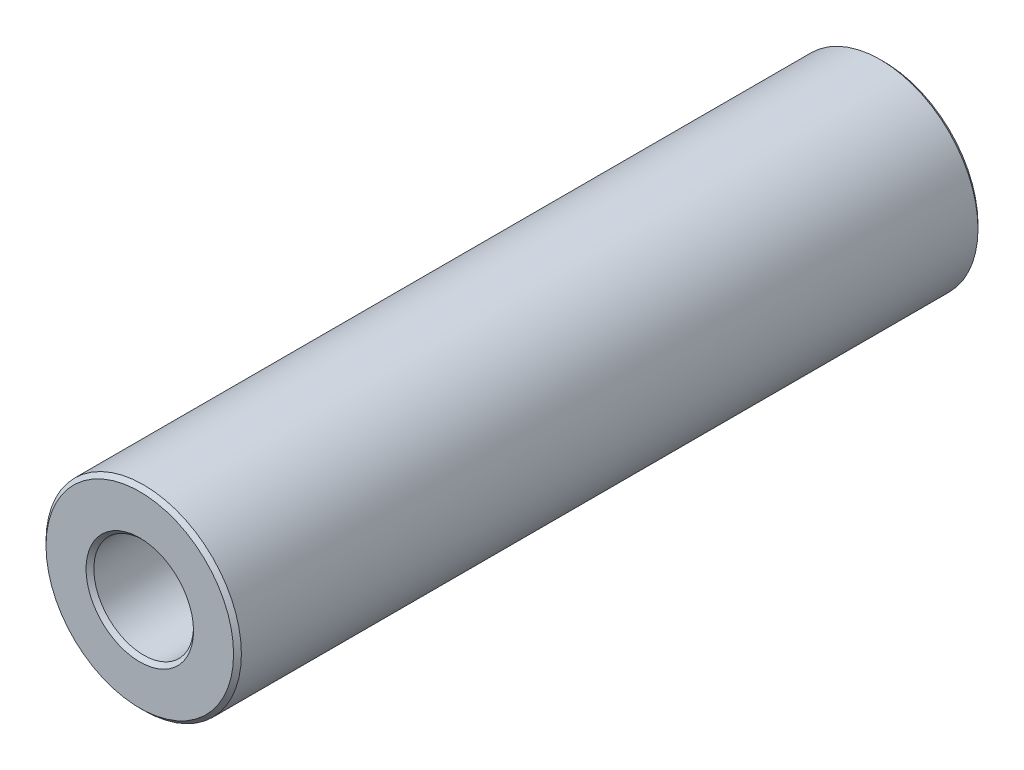
SolidWorks part; units mm, degrees
material "6061-T6 (SS)"
ref_plane "Front Plane" through (0, 0, 0) normal (0, 0, 1) x (1, 0, 0)
ref_plane "Top Plane" through (0, 0, 0) normal (0, 1, 0) x (1, 0, 0)
ref_plane "Right Plane" through (0, 0, 0) normal (1, 0, 0) x (0, 0, -1)
sketch "Sketch1" plane through (0, 0, 0) normal (0, 0, 1) x (1, 0, 0)
  circle A0 centre (0, 0) radius 2.55
  circle A1 centre (0, 0) radius 5
  dimension "D1" = 5.1
  dimension "D2" = 10
extrude "Boss-Extrude1" add sketch "Sketch1" along normal blind 38.1
chamfer "Chamfer1" distance 0.2 angle 45 4 edges at (5, 0, 0) (2.55, 0, 0) (2.55, 0, 38.1) (5, 0, 38.1)
